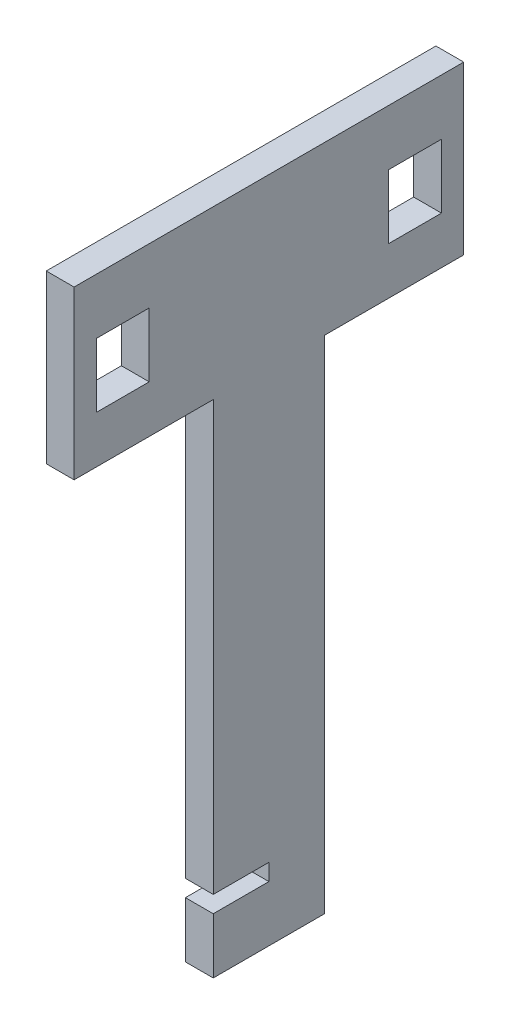
SolidWorks part; units mm, degrees
material "Very Low Density PE (SS)"
ref_plane "Front Plane" through (0, 0, 0) normal (0, 0, 1) x (1, 0, 0)
ref_plane "Top Plane" through (0, 0, 0) normal (0, 1, 0) x (1, 0, 0)
ref_plane "Right Plane" through (0, 0, 0) normal (1, 0, 0) x (0, 0, -1)
sketch "Sketch1" plane through (0, 0, 0) normal (0, 0, 1) x (1, 0, 0)
  line L0 (5, 0) -> (5, 120)
  line L1 (0, 0) -> (0, 120)
  line L6 (0, 0) -> (5, 0)
  line L8 (0, 120) -> (5, 120)
  line L10 (5, 5) -> (5, 8)
  dimension "D2" = 120
extrude "Boss-Extrude1" add sketch "Sketch1" along normal blind 70
sketch "Sketch2" plane through (5, 0, 0) normal (1, 0, 0) x (0, 0, -1)
  line L0 (-70, 0) -> (-70, 120) construction
  line L1 (-70, 10) -> (-35, 10)
  line L2 (-70, 10) -> (-70, 13)
  line L3 (-70, 13) -> (-35, 13)
  line L4 (-35, 10) -> (-35, 13)
  line L5 (-70, 0) -> (0, 0) construction
  line L6 (-35, 120) -> (-35, 0) construction
  line L8 (-70, 120) -> (0, 120) construction
  point P10 (-25, 120)
  dimension "D2" = 3
  dimension "D3" = 10
extrude "Cut-Extrude1" cut sketch "Sketch2" against normal through all
sketch "Sketch3" plane through (0, 0, 0) normal (1, 0, 0) x (0, 0, -1)
  line L0 (-35, 120) -> (-35, 83.0202) construction
  line L1 (-13.5, 110) -> (-4, 110)
  line L2 (-13.5, 110) -> (-13.5, 98.5)
  line L3 (-13.5, 98.5) -> (-4, 98.5)
  line L4 (-4, 110) -> (-4, 98.5)
  line L7 (-70, 120) -> (0, 120) construction
  line L8 (-56.5, 98.5) -> (-66, 98.5)
  line L9 (-66, 110) -> (-66, 98.5)
  line L10 (-56.5, 110) -> (-66, 110)
  line L11 (-56.5, 110) -> (-56.5, 98.5)
  line L12 (0, 0) -> (0, 120) construction
  point P4 (-25, 110)
  point P5 (-25, 120)
  dimension "D1" = 11.5
  dimension "D2" = 9.5
  dimension "D3" = 10
  dimension "D4" = 4
extrude "Cut-Extrude2" cut sketch "Sketch3" along normal through all from surface at 0 starting at face at (0, 35.75, 43.75)
sketch "Sketch5" plane through (5, 0, 0) normal (1, 0, 0) x (0, 0, -1)
  line L0 (-70, 13) -> (-70, 120) construction
  line L1 (-70, 90) -> (-45, 90)
  line L2 (-70, 90) -> (-70, 0)
  line L3 (-70, 0) -> (-45, 0)
  line L4 (-45, 90) -> (-45, 0)
  line L5 (-70, 0) -> (0, 0) construction
  line L6 (-35, 120) -> (-35, 0) construction
  line L7 (-70, 120) -> (0, 120) construction
  line L8 (0, 0) -> (-25, 0)
  line L9 (-25, 90) -> (-25, 0)
  line L10 (0, 90) -> (-25, 90)
  line L11 (0, 90) -> (0, 0)
  dimension "D1" = 25
  dimension "D2" = 90
extrude "Cut-Extrude3" cut sketch "Sketch5" against normal blind 10
